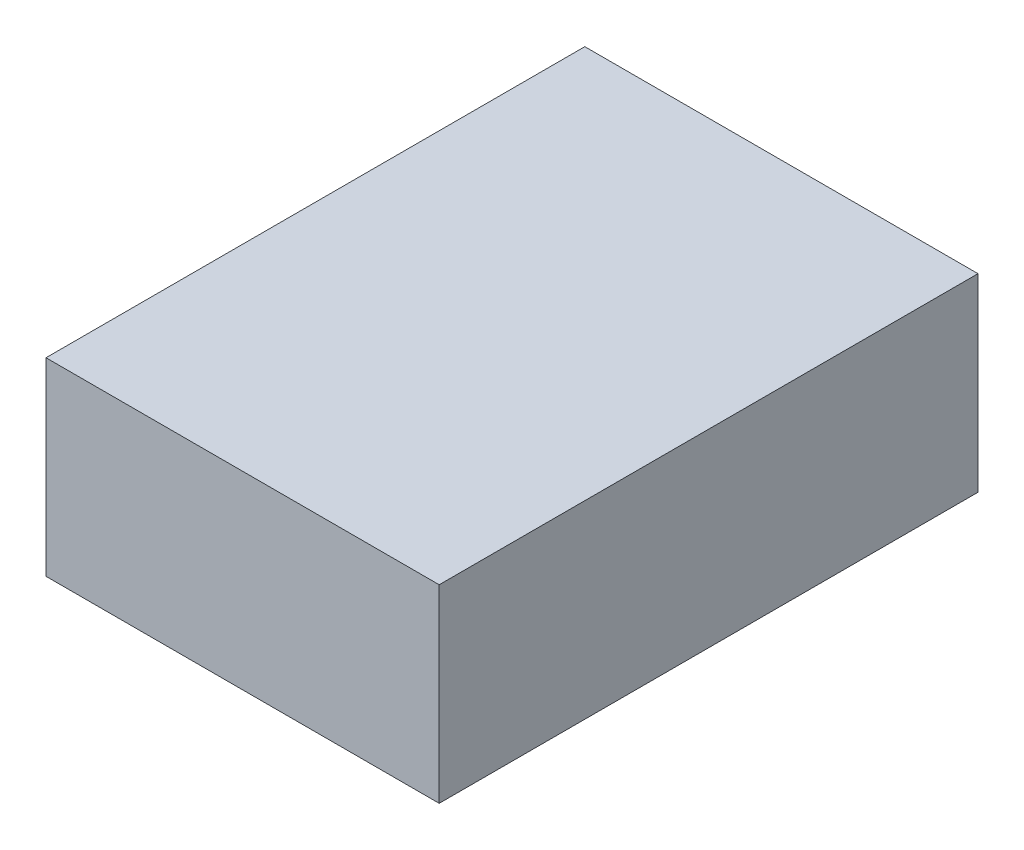
SolidWorks part; units mm, degrees
ref_plane "Front Plane" through (0, 0, 0) normal (0, 0, 1) x (1, 0, 0)
ref_plane "Top Plane" through (0, 0, 0) normal (0, 1, 0) x (1, 0, 0)
ref_plane "Right Plane" through (0, 0, 0) normal (1, 0, 0) x (0, 0, -1)
sketch "Sketch1" plane through (0, 0, 0) normal (0, 1, 0) x (1, 0, 0)
  line L0 (0, 18.5) -> (0, -18.5) construction
  line L1 (-13.5, 18.5) -> (13.5, 18.5)
  line L2 (-13.5, 18.5) -> (-13.5, -18.5)
  line L3 (-13.5, -18.5) -> (13.5, -18.5)
  line L4 (13.5, 18.5) -> (13.5, -18.5)
  line L5 (13.5, 0) -> (-13.5, 0) construction
  point P8 (0, 0)
  dimension "D1" = 27
  dimension "D2" = 37
extrude "Boss-Extrude1" add sketch "Sketch1" along normal blind 13
